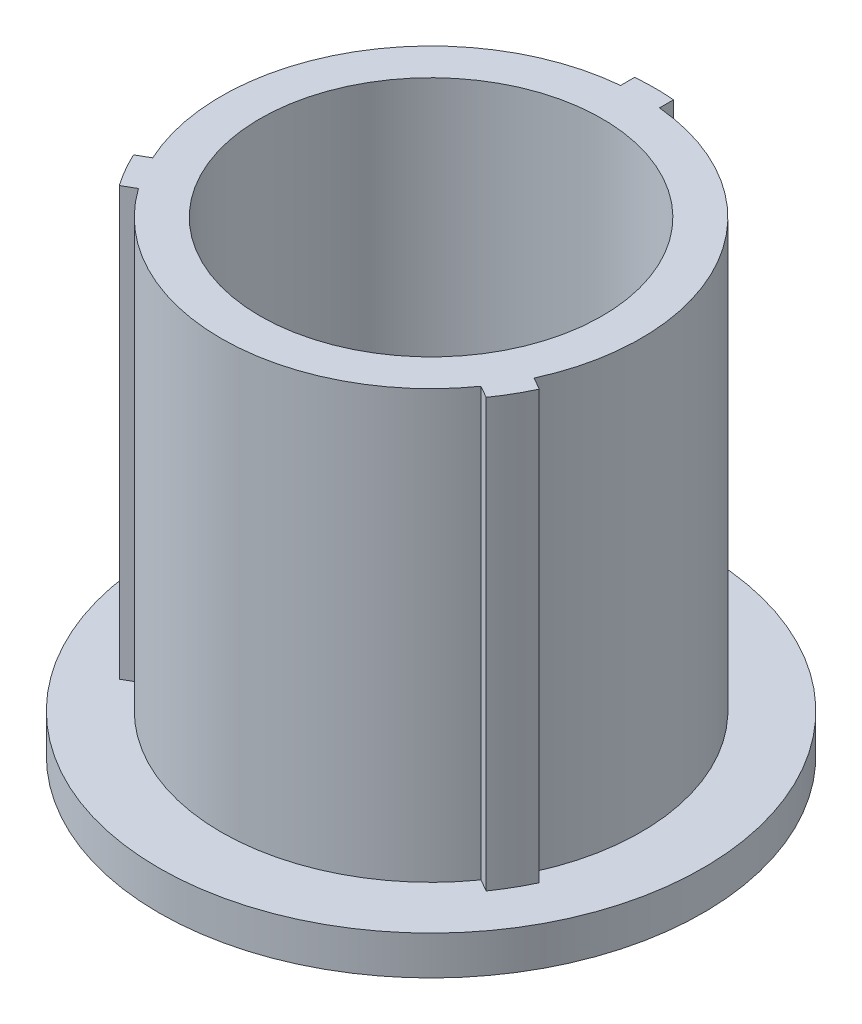
SolidWorks part; units mm, degrees
ref_plane "Front Plane" through (0, 0, 0) normal (0, 0, 1) x (1, 0, 0)
ref_plane "Top Plane" through (0, 0, 0) normal (0, 1, 0) x (1, 0, 0)
ref_plane "Right Plane" through (0, 0, 0) normal (1, 0, 0) x (0, 0, -1)
sketch "Sketch1" plane through (0, 0, 0) normal (0, 1, 0) x (1, 0, 0)
  line L0 (-0.7938, 9.1095) -> (-0.7938, 8.5357)
  line L1 (0.7937, 9.1095) -> (0.7937, 8.5357)
  line L2 (8.2859, -3.8673) -> (7.789, -3.5804)
  line L3 (7.4922, -5.2421) -> (6.9952, -4.9552)
  line L4 (-7.4922, -5.2421) -> (-6.9952, -4.9552)
  line L5 (-8.2859, -3.8673) -> (-7.789, -3.5804)
  arc A0 (-6.9952, -4.9552) -> (6.9952, -4.9552) centre (0, 0) ccw
  arc A1 (-8.2859, -3.8673) -> (-7.4922, -5.2421) centre (0, 0) ccw
  arc A2 (0.7937, 9.1095) -> (-0.7938, 9.1095) centre (0, 0) ccw
  arc A3 (7.4922, -5.2421) -> (8.2859, -3.8673) centre (0, 0) ccw
  arc A4 (7.789, -3.5804) -> (0.7937, 8.5357) centre (0, 0) ccw
  arc A5 (-0.7938, 8.5357) -> (-7.789, -3.5804) centre (0, 0) ccw
  point P18 (0, 0)
  dimension "D1" = 17.145
  dimension "D2" = 18.288
  dimension "D3" = 1.5875
  dimension "D4" = 3
extrude "Boss-Extrude1" add sketch "Sketch1" along normal blind 19.05
sketch "Sketch6" plane through (0, 0, 0) normal (1, 0, 0) x (0, 0, -1)
  line L0 (8.5357, 1.5875) -> (9.144, 1.5875)
  line L1 (8.5357, 1.5875) -> (8.5357, 0)
  line L3 (8.5357, 0) -> (9.144, 0)
  line L5 (9.144, 0) -> (9.144, 1.5875)
  line L6 (0, 19.7302) -> (0, -0.9338) construction
  dimension "D1" = 1.5875
revolve "Cut-Revolve2" cut sketch "Sketch6" angle 360 about L6
sketch "Sketch8" plane through (0, 0, 0) normal (1, 0, 0) x (0, 0, -1)
  line L1 (8.5357, 1.5875) -> (11.1125, 1.5875)
  line L2 (8.5357, 1.5875) -> (8.5357, 0)
  line L3 (8.5357, 0) -> (11.1125, 0)
  line L4 (11.1125, 1.5875) -> (11.1125, 0)
  line L8 (0, 4.4839) -> (0, -1.895) construction
  dimension "D1" = 11.1125
revolve "Revolve2" add sketch "Sketch8" angle 360 about L8
sketch "Sketch12" plane through (0, 19.05, 0) normal (0, 1, 0) x (1, 0, 0)
  circle A0 centre (0, 0) radius 6.985
  dimension "D1" = 13.97
extrude "Cut-Extrude7" cut sketch "Sketch12" against normal blind 17.018
sketch "Sketch13" plane through (0, 0, 0) normal (0, -1, 0) x (1, 0, 0)
  circle A0 centre (0, 0) radius 4.826
  dimension "D1" = 9.652
extrude "Cut-Extrude8" cut sketch "Sketch13" against normal through all
